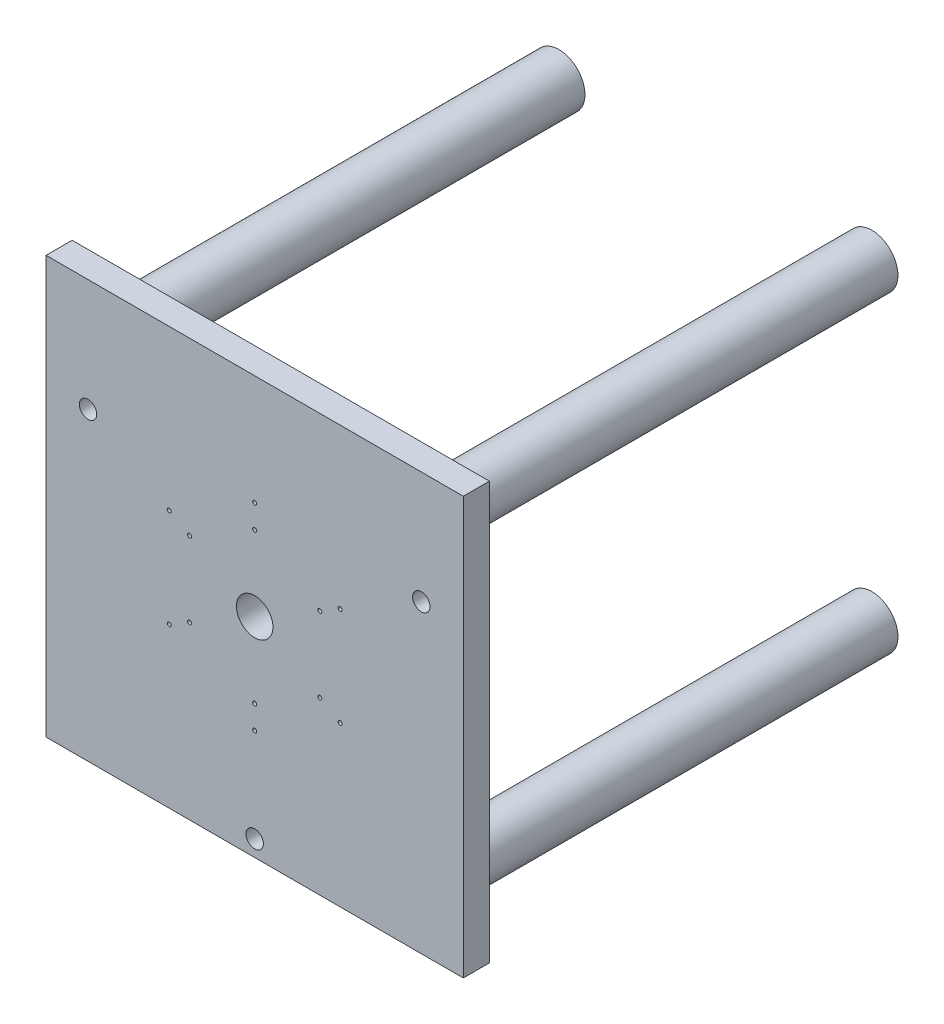
SolidWorks part; units mm, degrees
ref_plane "Front Plane" through (0, 0, 0) normal (0, 0, 1) x (1, 0, 0)
ref_plane "Top Plane" through (0, 0, 0) normal (0, 1, 0) x (1, 0, 0)
ref_plane "Right Plane" through (0, 0, 0) normal (1, 0, 0) x (0, 0, -1)
sketch "Sketch1" plane through (0, 0, 0) normal (0, 0, 1) x (1, 0, 0)
  line L1 (-120, 120) -> (120, 120)
  line L2 (-120, 120) -> (-120, -120)
  line L3 (-120, -120) -> (120, -120)
  line L4 (120, 120) -> (120, -120)
  line L5 (-120, 120) -> (120, -120) construction
  line L6 (-120, -120) -> (120, 120) construction
  point P0 (0, 0)
  dimension "D1" = 240
  dimension "D2" = 240
extrude "Boss-Extrude1" add sketch "Sketch1" along normal blind 15
sketch "Sketch3" plane through (0, 0, 0) normal (0, 0, -1) x (-1, 0, 0)
  line L0 (-120, 120) -> (120, -120) construction
  line L1 (120, 120) -> (-120, -120) construction
  line L2 (90, -90) -> (90, 90) construction
  line L3 (90, 90) -> (-90, 90) construction
  line L4 (-90, 90) -> (-90, -90) construction
  line L5 (-90, -90) -> (90, -90) construction
  line L6 (120, -120) -> (-120, -120) construction
  circle A0 centre (90, -90) radius 15
  dimension "D2" = 30
  dimension "D1" = 30
extrude "Boss-Extrude3" add sketch "Sketch3" along normal blind 250
mirror "Mirror6" about plane through (0, 0, 0) normal (0, 1, 0) of "Boss-Extrude3"
mirror "Mirror7" about plane through (0, 0, 0) normal (1, 0, 0) of "Boss-Extrude3", "Mirror6"
sketch "Sketch4" plane through (0, 0, 15) normal (0, 0, 1) x (1, 0, 0)
  circle A0 centre (0, 0) radius 10.5
  dimension "D1" = 21
extrude "Cut-Extrude1" cut sketch "Sketch4" against normal blind 250
sketch "Sketch5" plane through (0, 0, 15) normal (0, 0, 1) x (1, 0, 0)
  line L0 (43.3013, 25) -> (0, 0) construction
  line L1 (0, -50) -> (43.3013, -25)
  line L2 (43.3013, -25) -> (43.3013, 25)
  line L3 (43.3013, 25) -> (0, 50)
  line L4 (0, 50) -> (-43.3013, 25)
  line L5 (-43.3013, 25) -> (-43.3013, -25)
  line L6 (-43.3013, -25) -> (0, -50)
  line L7 (0, 0) -> (0, 50) construction
  line L8 (0, 0) -> (-43.3013, 25) construction
  line L9 (0, 0) -> (-43.3013, -25) construction
  line L10 (0, 0) -> (0, -50) construction
  line L11 (0, 0) -> (43.3013, -25) construction
  line L12 (0, 50) -> (0, 56.75) construction
  line L13 (43.3013, 25) -> (49.1469, 28.375) construction
  circle A0 centre (0, 0) radius 50
  circle A1 centre (0, 0) radius 43.3013 construction
  circle A2 centre (0, 43.25) radius 1.15
  circle A3 centre (0, 56.75) radius 1.15
  circle A4 centre (37.4556, 21.625) radius 1.15
  circle A5 centre (49.1469, 28.375) radius 1.15
  dimension "D1" = 100
  dimension "D5" = 2.3
  dimension "D8" = 2.3
  dimension "D10" = 2.3
  dimension "D13" = 2.3
  dimension "D2" = 50
  dimension "D3" = 43.3013
  dimension "D4" = 6.75
  dimension "D6" = 6.75
  dimension "D7" = 180
  dimension "D9" = 6.75
  dimension "D11" = 6.75
  dimension "D12" = 180
extrude "Cut-Extrude2" cut sketch "Sketch5" against normal blind 40 contours A4 | A5 | A2 | A3
mirror "Mirror8" about plane through (0, 0, 0) normal (0, 1, 0) of "Cut-Extrude2"
mirror "Mirror9" about plane through (0, 0, 0) normal (1, 0, 0) of "Mirror8", "Cut-Extrude2"
sketch "Sketch6" plane through (0, 0, 15) normal (0, 0, 1) x (1, 0, 0)
  line L0 (0, 0) -> (0, -110.68) construction
  line L1 (0, 0) -> (95.8517, 55.34) construction
  line L2 (0, 0) -> (-95.8517, 55.34) construction
  circle A0 centre (0, -110.68) radius 5
  circle A1 centre (-95.8517, 55.34) radius 5
  circle A2 centre (95.8517, 55.34) radius 5
  dimension "D6" = 10
  dimension "D7" = 10
  dimension "D8" = 10
  dimension "D1" = 120
  dimension "D2" = 120
  dimension "D3" = 110.68
  dimension "D4" = 110.68
  dimension "D5" = 110.68
extrude "Cut-Extrude3" cut sketch "Sketch6" against normal blind 30
